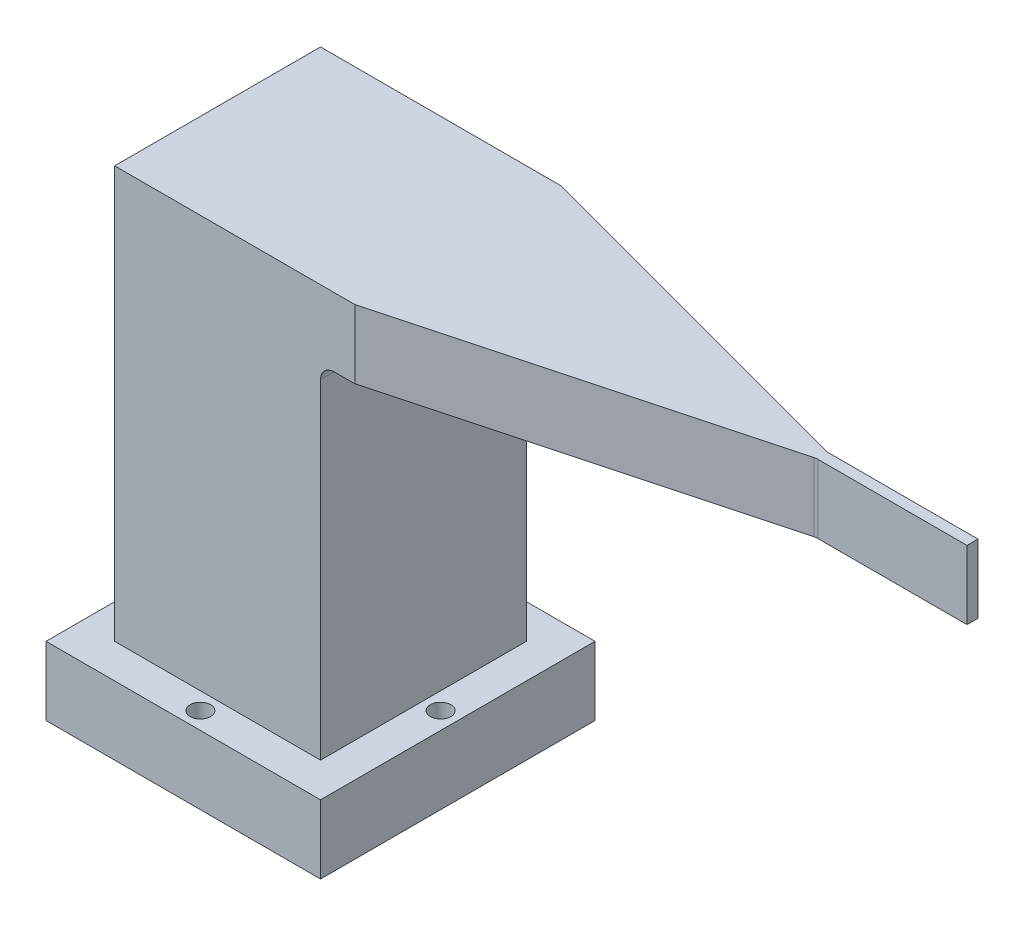
SolidWorks part; units mm, degrees
ref_plane "Plan de face" through (0, 0, 0) normal (0, 0, 1) x (1, 0, 0)
ref_plane "Plan de dessus" through (0, 0, 0) normal (0, 1, 0) x (1, 0, 0)
ref_plane "Plan de droite" through (0, 0, 0) normal (1, 0, 0) x (0, 0, -1)
sketch "Esquisse1" plane through (0, 0, 0) normal (0, 1, 0) x (1, 0, 0)
  line L1 (10, -10) -> (-10, -10)
  line L2 (10, -10) -> (10, 10)
  line L3 (10, 10) -> (-10, 10)
  line L4 (-10, -10) -> (-10, 10)
  line L5 (10, -10) -> (-10, 10) construction
  line L6 (10, 10) -> (-10, -10) construction
  point P0 (0, 0)
  dimension "D1" = 20
  dimension "D2" = 20
extrude "Boss.-Extru.1" add sketch "Esquisse1" along normal blind 5
sketch "Esquisse2" plane through (0, 0, 0) normal (0, -1, 0) x (-1, 0, 0)
  line L1 (-7.5, 7.5) -> (7.5, 7.5)
  line L2 (-7.5, 7.5) -> (-7.5, -7.5)
  line L3 (-7.5, -7.5) -> (7.5, -7.5)
  line L4 (7.5, 7.5) -> (7.5, -7.5)
  line L5 (-7.5, 7.5) -> (7.5, -7.5) construction
  line L6 (-7.5, -7.5) -> (7.5, 7.5) construction
  point P0 (0, 0)
  dimension "D1" = 15
  dimension "D2" = 15
extrude "Boss.-Extru.2" add sketch "Esquisse2" against normal blind 35
sketch "Esquisse3" plane through (0, 5, 0) normal (0, 1, 0) x (1, 0, 0)
  circle A0 centre (-8.75, 0) radius 0.75
  circle A1 centre (0, 8.75) radius 0.75
  circle A2 centre (8.75, 0) radius 0.75
  circle A3 centre (0, -8.75) radius 0.75
  point P12 (0, 0)
  dimension "D1" = 1.5
  dimension "D2" = 8.75
  dimension "D3" = 4
extrude "Enlèv. mat.-Extru.1" cut sketch "Esquisse3" against normal up to surface (5 mm away) up to face at (0, 0, 0)
sketch "Esquisse5" plane through (7.5, 0, 0) normal (1, 0, 0) x (0, 0, -1)
  line L0 (7.5, 35) -> (7.5, 5) construction
  line L1 (-7.5, 35) -> (7.5, 35)
  line L2 (-7.5, 35) -> (-7.5, 30)
  line L3 (-7.5, 30) -> (7.5, 30)
  line L4 (7.5, 35) -> (7.5, 30)
  dimension "D1" = 5
extrude "Boss.-Extru.3" add sketch "Esquisse5" along normal blind 40
sketch "Esquisse6" plane through (0, 35, 0) normal (0, 1, 0) x (1, 0, 0)
  line L0 (10, 7.5) -> (36.4976, 0.4)
  line L1 (-7.5, 7.5) -> (47.5, 7.5) construction
  line L2 (10, -10) -> (10, 10) construction
  line L4 (10, 7.5) -> (47.5, 7.5)
  line L10 (36.4976, 0.4) -> (47.5, 0.4)
  line L11 (47.5, 7.5) -> (47.5, -7.5) construction
  line L12 (47.5, 0.4) -> (47.5, 7.5)
  line L13 (-19.25, 0) -> (19.25, 0) construction
  line L14 (36.4976, -0.4) -> (47.5, -0.4)
  line L15 (10, -7.5) -> (36.4976, -0.4)
  line L16 (10, -7.5) -> (47.5, -7.5)
  line L17 (47.5, -0.4) -> (47.5, -7.5)
  dimension "D1" = 0.8
  dimension "D2" = 30
extrude "Enlèv. mat.-Extru.2" cut sketch "Esquisse6" against normal up to surface (5 mm away) up to face at (27.5, 30, 0)
fillet "Congé1" radius 1 3 edges at (7.5, 30, 0) (36.4976, 32.5, -0.4) (36.4976, 32.5, 0.4)
